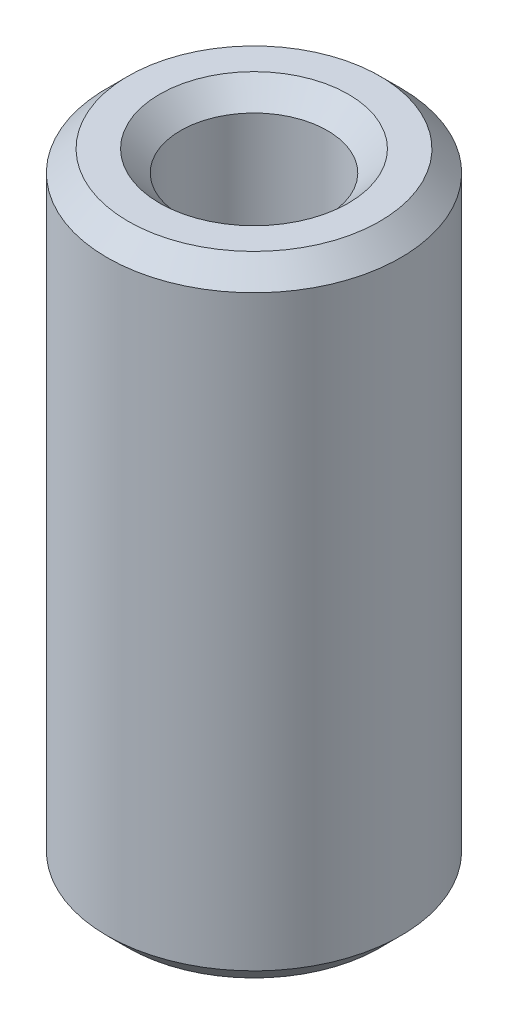
SolidWorks part; units mm, degrees
ref_plane "Front Plane" through (0, 0, 0) normal (0, 0, 1) x (1, 0, 0)
ref_plane "Top Plane" through (0, 0, 0) normal (0, 1, 0) x (1, 0, 0)
ref_plane "Right Plane" through (0, 0, 0) normal (1, 0, 0) x (0, 0, -1)
sketch "Sketch1" plane through (0, 0, 0) normal (0, 1, 0) x (1, 0, 0)
  circle A0 centre (0, 0) radius 3.5
  circle A1 centre (0, 0) radius 1.75
  dimension "D1" = 7
  dimension "D2" = 3.5
extrude "Boss-Extrude1" add sketch "Sketch1" along normal blind 15
chamfer "Chamfer1" distance 0.5 angle 45 4 edges at (0, 0, 1.75) (0, 0, 3.5) (0, 15, 1.75) (0, 15, 3.5)
